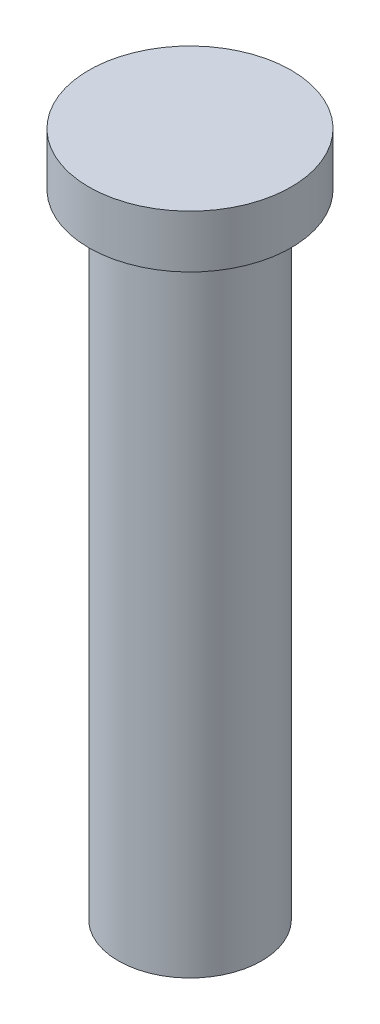
SolidWorks part; units mm, degrees
ref_plane "Front Plane" through (0, 0, 0) normal (0, 0, 1) x (1, 0, 0)
ref_plane "Top Plane" through (0, 0, 0) normal (0, 1, 0) x (1, 0, 0)
ref_plane "Right Plane" through (0, 0, 0) normal (1, 0, 0) x (0, 0, -1)
sketch "Sketch1" plane through (0, 0, 0) normal (0, 1, 0) x (1, 0, 0)
  circle A0 centre (0, 0) radius 1.7
  dimension "D1" = 3.4
extrude "Boss-Extrude1" add sketch "Sketch1" along normal blind 15
sketch "Sketch2" plane through (0, 15, 0) normal (0, 1, 0) x (1, 0, 0)
  circle A0 centre (0, 0) radius 2.4
  dimension "D1" = 4.8
extrude "Boss-Extrude2" add sketch "Sketch2" along normal blind 1.25 contours A0
